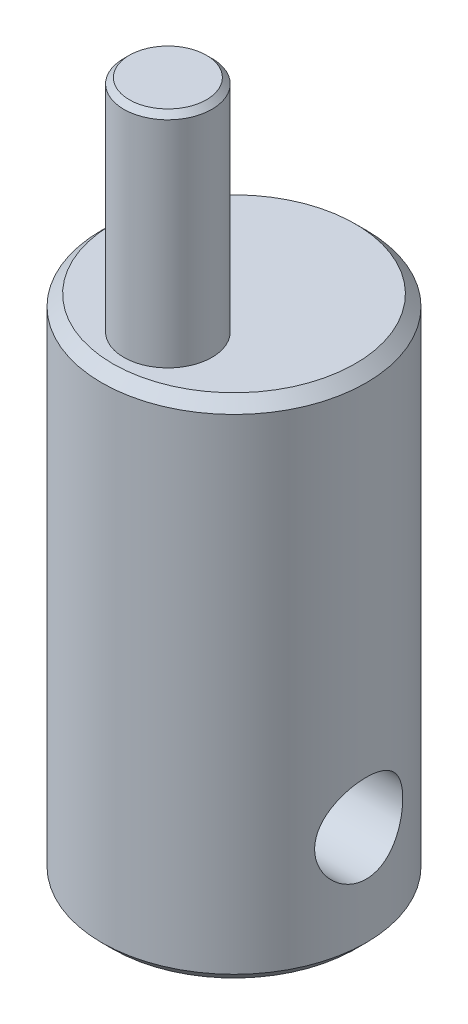
SolidWorks part; units mm, degrees
material "Stainless Steel (ferritic)"
ref_plane "Front Plane" through (0, 0, 0) normal (0, 0, 1) x (1, 0, 0)
ref_plane "Top Plane" through (0, 0, 0) normal (0, 1, 0) x (1, 0, 0)
ref_plane "Right Plane" through (0, 0, 0) normal (1, 0, 0) x (0, 0, -1)
sketch "Sketch1" plane through (0, 0, 0) normal (0, 1, 0) x (1, 0, 0)
  circle A0 centre (0, 0) radius 3
  dimension "D1" = 6
extrude "Boss-Extrude1" add sketch "Sketch1" along normal blind 11.5
sketch "Sketch4" plane through (0, 11.5, 0) normal (0, 1, 0) x (1, 0, 0)
  line L0 (0, 3.2196) -> (0, -3.1956) construction
  circle A0 centre (0, -1.5) radius 1
  dimension "D2" = 2
  dimension "D1" = 1.5
extrude "Boss-Extrude2" add sketch "Sketch4" along normal blind 5
sketch "Sketch9" plane through (0, 0, 0) normal (1, 0, 0) x (0, 0, -1)
  line L0 (0, 11.5) -> (0, 0) construction
  circle A0 centre (0, 2.5) radius 1
  point P2 (0, 0)
  dimension "4/2" = 2
  dimension "5/2" = 2.5
extrude "Cut-Extrude1" cut sketch "Sketch9" against normal through all both and the other way through all contours A0
chamfer "Chamfer1" distance 0.25 angle 45 1 edges at (0, 11.5, 3)
chamfer "Chamfer2" distance 0.25 angle 45 1 edges at (0, 0, 3)
chamfer "Chamfer3" distance 0.125 angle 45 1 edges at (0, 16.5, 2.5)
